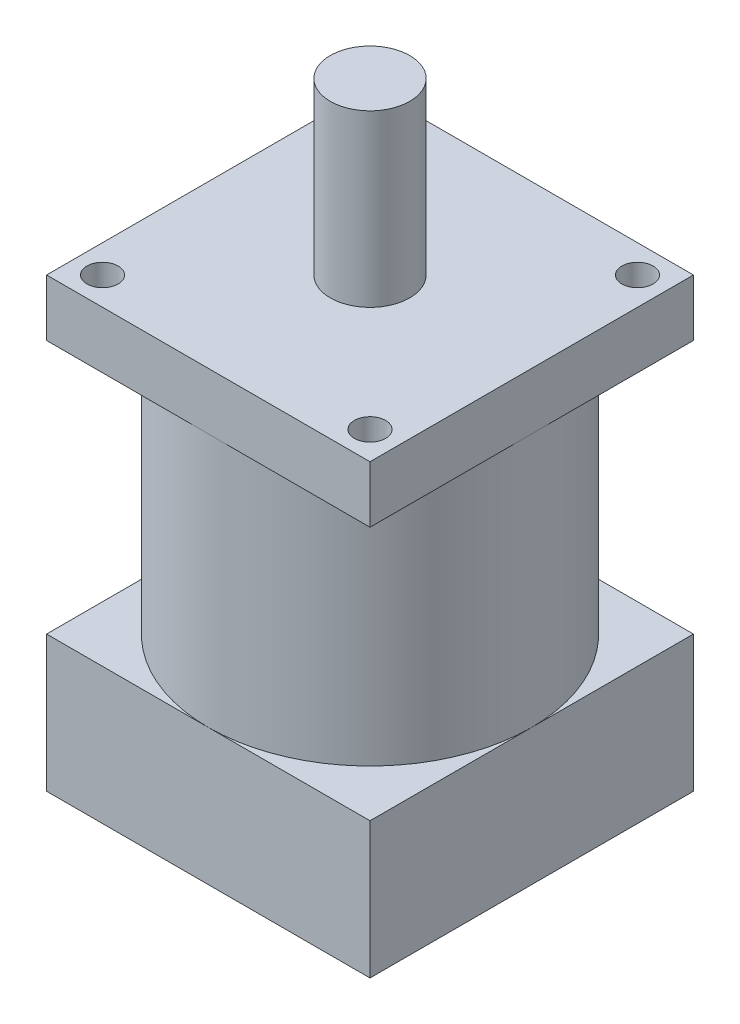
SolidWorks part; units mm, degrees
ref_plane "前视基准面" through (0, 0, 0) normal (0, 0, 1) x (1, 0, 0)
ref_plane "上视基准面" through (0, 0, 0) normal (0, 1, 0) x (1, 0, 0)
ref_plane "右视基准面" through (0, 0, 0) normal (1, 0, 0) x (0, 0, -1)
sketch "草图1" plane through (0, 0, 0) normal (0, 1, 0) x (1, 0, 0)
  line L1 (-28.5, 28.5) -> (28.5, 28.5)
  line L2 (-28.5, 28.5) -> (-28.5, -28.5)
  line L3 (-28.5, -28.5) -> (28.5, -28.5)
  line L4 (28.5, 28.5) -> (28.5, -28.5)
  line L5 (-28.5, 28.5) -> (28.5, -28.5) construction
  line L6 (-28.5, -28.5) -> (28.5, 28.5) construction
  point P0 (0, 0)
  dimension "D1" = 57
  dimension "D2" = 57
extrude "凸台-拉伸3" add sketch "草图1" along normal blind 24
ref_plane "基准面2" through (0, 24, 0) normal (0, 1, 0) x (1, 0, 0)
sketch "草图3" plane through (0, 24, 0) normal (0, 1, 0) x (1, 0, 0)
  circle A0 centre (0, 0) radius 28.5
extrude "凸台-拉伸4" add sketch "草图3" along normal blind 44.8
ref_plane "基准面3" through (0, 68.8, 0) normal (0, 1, 0) x (1, 0, 0)
sketch "草图4" plane through (0, 68.8, 0) normal (0, 1, 0) x (1, 0, 0)
  line L1 (-28.5, 28.5) -> (28.5, 28.5)
  line L2 (-28.5, 28.5) -> (-28.5, -28.5)
  line L3 (-28.5, -28.5) -> (28.5, -28.5)
  line L4 (28.5, 28.5) -> (28.5, -28.5)
  line L5 (-28.5, 28.5) -> (28.5, -28.5) construction
  line L6 (-28.5, -28.5) -> (28.5, 28.5) construction
  point P0 (0, 0)
extrude "凸台-拉伸5" add sketch "草图4" along normal blind 10
ref_plane "基准面4" through (0, 78.8, 0) normal (0, 1, 0) x (1, 0, 0)
sketch "草图6" plane through (0, 78.8, 0) normal (0, 1, 0) x (1, 0, 0)
  circle A0 centre (0, 0) radius 7
  dimension "D1" = 14
extrude "凸台-拉伸6" add sketch "草图6" along normal blind 30
sketch "草图7" plane through (0, 78.8, 0) normal (0, 1, 0) x (1, 0, 0)
  line L1 (-23.57, 23.57) -> (23.57, 23.57) construction
  line L2 (-23.57, 23.57) -> (-23.57, -23.57) construction
  line L3 (-23.57, -23.57) -> (23.57, -23.57) construction
  line L4 (23.57, 23.57) -> (23.57, -23.57) construction
  line L5 (-23.57, 23.57) -> (23.57, -23.57) construction
  line L6 (-23.57, -23.57) -> (23.57, 23.57) construction
  circle A0 centre (23.57, -23.57) radius 2.75
  circle A1 centre (-23.57, -23.57) radius 2.75
  circle A2 centre (-23.57, 23.57) radius 2.75
  circle A3 centre (23.57, 23.57) radius 2.75
  point P0 (0, 0)
  dimension "D3" = 5.5
  dimension "D4" = 5.5
  dimension "D5" = 5.5
  dimension "D6" = 5.5
  dimension "D1" = 47.14
  dimension "D2" = 47.14
extrude "切除-拉伸1" cut sketch "草图7" against normal blind 30
ref_plane "基准面5" through (0, 0, 0) normal (0, -1, 0) x (-1, 0, 0)
sketch "草图8" plane through (0, 0, 0) normal (0, -1, 0) x (-1, 0, 0)
  line L1 (-23.57, 23.57) -> (23.57, 23.57) construction
  line L2 (-23.57, 23.57) -> (-23.57, -23.57) construction
  line L3 (-23.57, -23.57) -> (23.57, -23.57) construction
  line L4 (23.57, 23.57) -> (23.57, -23.57) construction
  line L5 (-23.57, 23.57) -> (23.57, -23.57) construction
  line L6 (-23.57, -23.57) -> (23.57, 23.57) construction
  circle A0 centre (23.57, 23.57) radius 2
  circle A1 centre (-23.57, 23.57) radius 2
  circle A2 centre (-23.57, -23.57) radius 2
  circle A3 centre (23.57, -23.57) radius 2
  point P0 (0, 0)
  dimension "D3" = 4
  dimension "D4" = 4
  dimension "D5" = 4
  dimension "D6" = 4
  dimension "D1" = 47.14
  dimension "D2" = 47.14
extrude "切除-拉伸2" cut sketch "草图8" against normal blind 5
